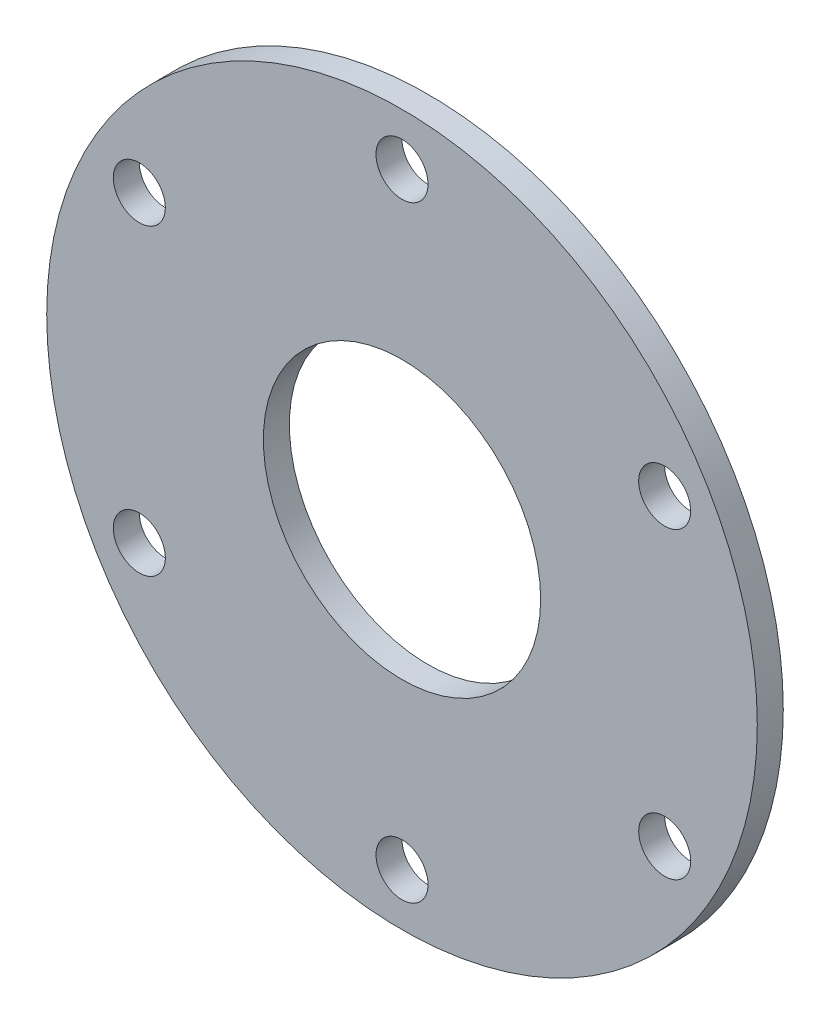
SolidWorks part; units mm, degrees
ref_plane "Front Plane" through (0, 0, 0) normal (0, 0, 1) x (1, 0, 0)
ref_plane "Top Plane" through (0, 0, 0) normal (0, 1, 0) x (1, 0, 0)
ref_plane "Right Plane" through (0, 0, 0) normal (1, 0, 0) x (0, 0, -1)
sketch "Sketch1" plane through (0, 0, 0) normal (0, 0, 1) x (1, 0, 0)
  circle A0 centre (0, 0) radius 41
  circle A1 centre (0, 0) radius 35 construction
  dimension "D1" = 82
  dimension "D2" = 70
extrude "Boss-Extrude1" add sketch "Sketch1" along normal blind 3
sketch "Sketch3" plane through (0, 0, 0) normal (0, 0, -1) x (-1, 0, 0)
  circle A0 centre (0, 35) radius 3
  circle A1 centre (0, 0) radius 35 construction
  dimension "D1" = 6
extrude "Cut-Extrude1" cut sketch "Sketch3" against normal through all
pattern_circular "CirPattern1" count 6 over 360 about axis through (0, 0, 0) along (0, 0, 1) of "Cut-Extrude1"
sketch "Sketch4" plane through (0, 0, 3) normal (0, 0, 1) x (1, 0, 0)
  circle A0 centre (0, 0) radius 16
  dimension "D1" = 32
extrude "Cut-Extrude2" cut sketch "Sketch4" against normal up to next
